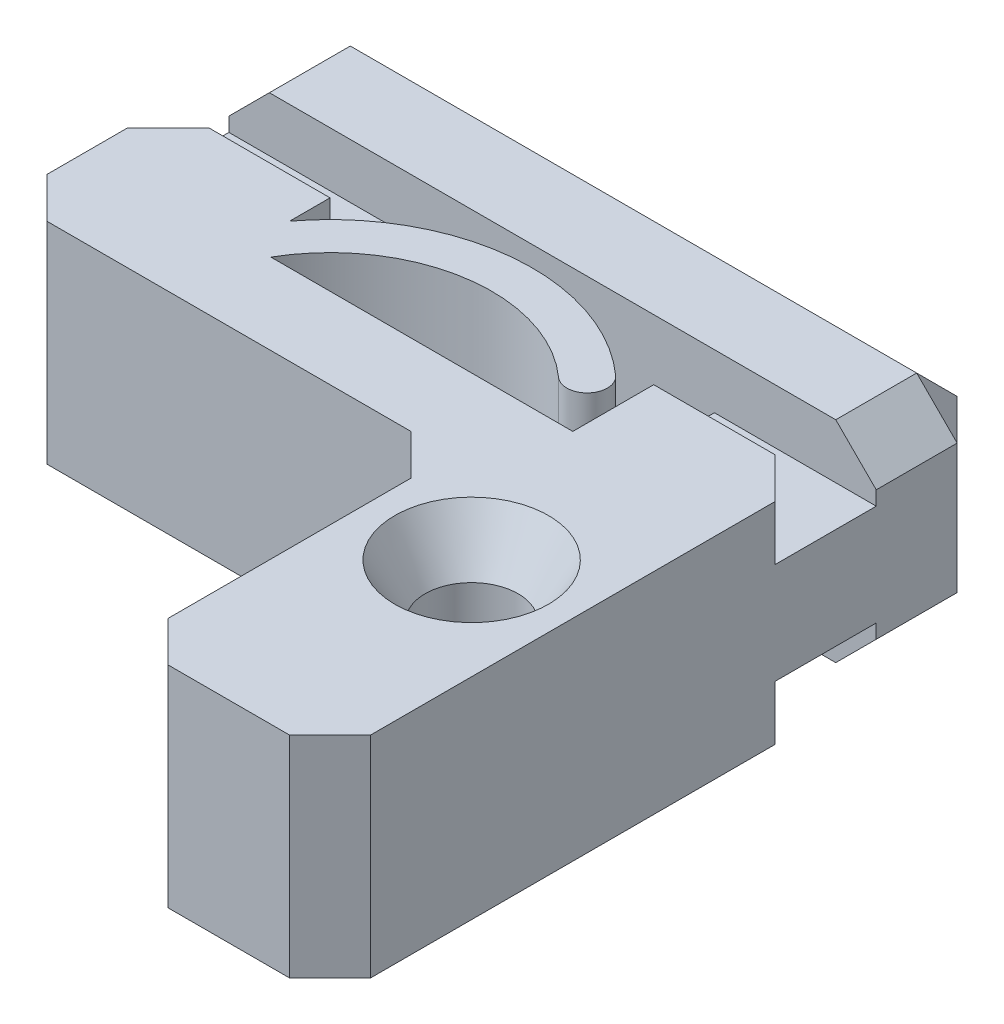
SolidWorks part; units mm, degrees
ref_plane "Front Plane" through (0, 0, 0) normal (0, 0, 1) x (1, 0, 0)
ref_plane "Top Plane" through (0, 0, 0) normal (0, 1, 0) x (1, 0, 0)
ref_plane "Right Plane" through (0, 0, 0) normal (1, 0, 0) x (0, 0, -1)
sketch "Sketch1" plane through (0, 0, 0) normal (0, 1, 0) x (1, 0, 0)
  line L0 (4, 0) -> (8, 0)
  line L1 (-8, 0) -> (-4, 0)
  line L2 (-8, 0) -> (-8, -4)
  line L3 (-8, -4) -> (3, -4)
  line L4 (8, 0) -> (8, -12)
  line L5 (3, -4) -> (3, -12)
  line L6 (-4, 0) -> (-4, -2)
  line L7 (-4, -2) -> (4, -2)
  line L8 (4, 0) -> (4, -2)
  line L9 (3, -12) -> (8, -12)
  circle A0 centre (5.5, -6) radius 1.15
  point P4 (0, -2)
  point P14 (5.5, -12)
  point P15 (8, -6)
  dimension "D7" = 2.3
  dimension "D1" = 8
  dimension "D2" = 2
  dimension "D3" = 16
  dimension "D4" = 4
  dimension "D5" = 12
  dimension "D6" = 5
extrude "Boss-Extrude1" add sketch "Sketch1" along normal mid plane 5.2
sketch "Sketch2" plane through (-8, 0, 0) normal (-1, 0, 0) x (0, 0, 1)
  line L0 (-1.5, -1.25) -> (-1.5, -2.6)
  line L1 (-4.5, 2.6) -> (-1.5, 2.6)
  line L2 (-4.5, 2.6) -> (-4.5, -2.6)
  line L3 (-4.5, -2.6) -> (-1.5, -2.6)
  line L4 (-1.5, 2.6) -> (-1.5, 1.25)
  line L5 (-1.5, 1.25) -> (0, 1.25)
  line L6 (0, 2.6) -> (0, -2.6) construction
  line L7 (-1.5, -1.25) -> (0, -1.25)
  line L8 (0, 1.25) -> (0, -1.25)
  line L9 (0, 2.6) -> (4, 2.6) construction
  line L10 (0, -2.6) -> (4, -2.6) construction
  point P6 (0, 0)
  dimension "D1" = 3
  dimension "D2" = 1.5
  dimension "D3" = 2.5
extrude "Boss-Extrude2" add sketch "Sketch2" against normal blind 4
mirror "Mirror1" about plane through (0, 0, 0) normal (1, 0, 0) of "Boss-Extrude2"
sketch "Sketch3" plane through (-4, 0, 0) normal (1, 0, 0) x (0, 0, -1)
  line L1 (4.5, -2.6) -> (1.5, -2.6)
  line L2 (4.5, -2.6) -> (4.5, 2.6)
  line L3 (4.5, 2.6) -> (1.5, 2.6)
  line L4 (1.5, -2.6) -> (1.5, 2.6)
extrude "Boss-Extrude3" add sketch "Sketch3" along normal blind 8
sketch "Sketch4" plane through (0, 0, 0) normal (0, 1, 0) x (1, 0, 0)
  line L0 (-4, -1) -> (-4, -2)
  line L1 (-4, -2) -> (-3.4641, -2)
  line L2 (4, -2) -> (-4, -2) construction
  line L3 (4, 0) -> (4, -2) construction
  arc A0 (-4, -1) -> (3.3333, -0.2732) centre (0, -4) cw
  arc A1 (3.3333, -0.2732) -> (2.6667, -1.0186) centre (3, -0.6459) cw
  arc A2 (-3.4641, -2) -> (2.6667, -1.0186) centre (0, -4) cw
  dimension "D1" = 1
  dimension "D4" = 5
  dimension "D2" = 2
  dimension "D3" = 0.5
extrude "Boss-Extrude4" add sketch "Sketch4" along normal mid plane 5.2
chamfer "Chamfer1" distance 1 angle 45 12 edges at (-8, 1.925, 0) (8, 1.925, 0) (8, 0, 12) (3, 0, 12) (3, 0, 4) (-8, 0, 4) (-8, -1.925, 0) (0, -2.6, -4.5) (0, 2.6, -4.5) (-8, 0, -4.5) (8, -1.925, 0) (8, 0, -4.5)
chamfer "Chamfer2" distance 0.75 angle 60 2 edges at (5.5, -2.6, 7.15) (5.5, 2.6, 7.15)
